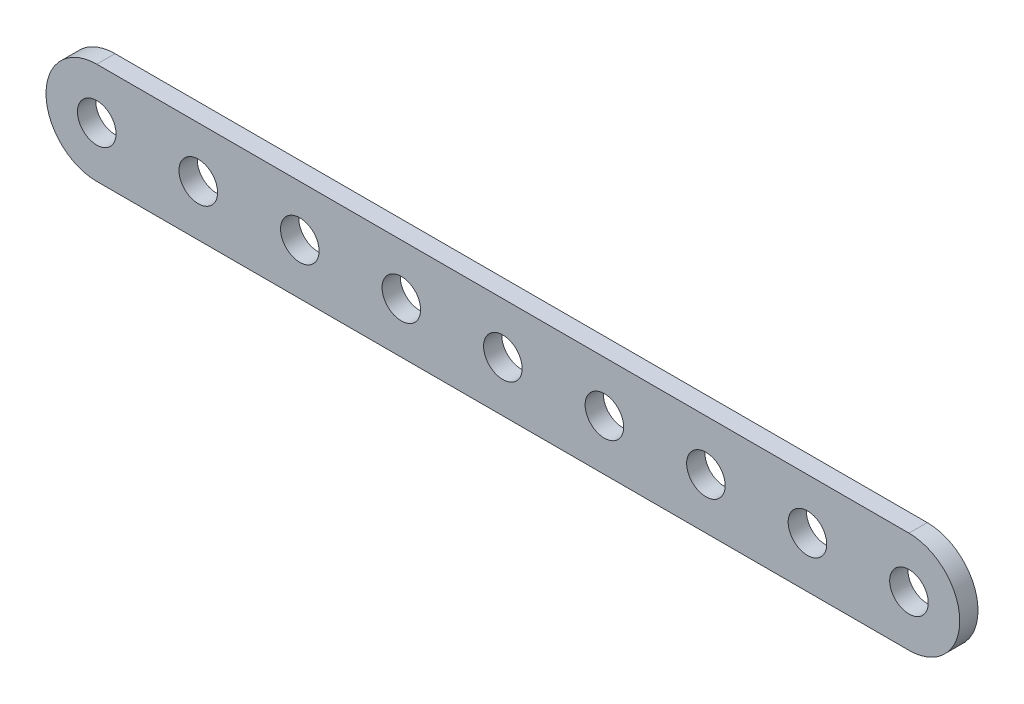
SolidWorks part; units mm, degrees
material "2014 Alloy"
ref_plane "Front Plane" through (0, 0, 0) normal (0, 0, 1) x (1, 0, 0)
ref_plane "Top Plane" through (0, 0, 0) normal (0, 1, 0) x (1, 0, 0)
ref_plane "Right Plane" through (0, 0, 0) normal (1, 0, 0) x (0, 0, -1)
sketch "Sketch1" plane through (0, 0, 0) normal (0, 0, 1) x (1, 0, 0)
  line L0 (-50.8, 0) -> (50.8, 0) construction
  line L1 (-50.8, -6.35) -> (50.8, -6.35)
  line L3 (-50.8, 6.35) -> (50.8, 6.35)
  arc A0 (50.8, 6.35) -> (50.8, -6.35) centre (50.8, 0) cw
  arc A1 (-50.8, 6.35) -> (-50.8, -6.35) centre (-50.8, 0) ccw
  dimension "D2" = 6.35
  dimension "D1" = 101.6
extrude "Extrude1" add sketch "Sketch1" along normal blind 2.286
sketch "Sketch2" plane through (0, 0, 2.286) normal (0, 0, 1) x (1, 0, 0)
  circle A0 centre (-50.8, 0) radius 2.413
  dimension "D1" = 4.826
extrude "Cut-Extrude1" cut sketch "Sketch2" against normal through all
pattern_linear "LPattern1" count 9 spacing 12.7 along (1, 0, 0) of "Cut-Extrude1"
